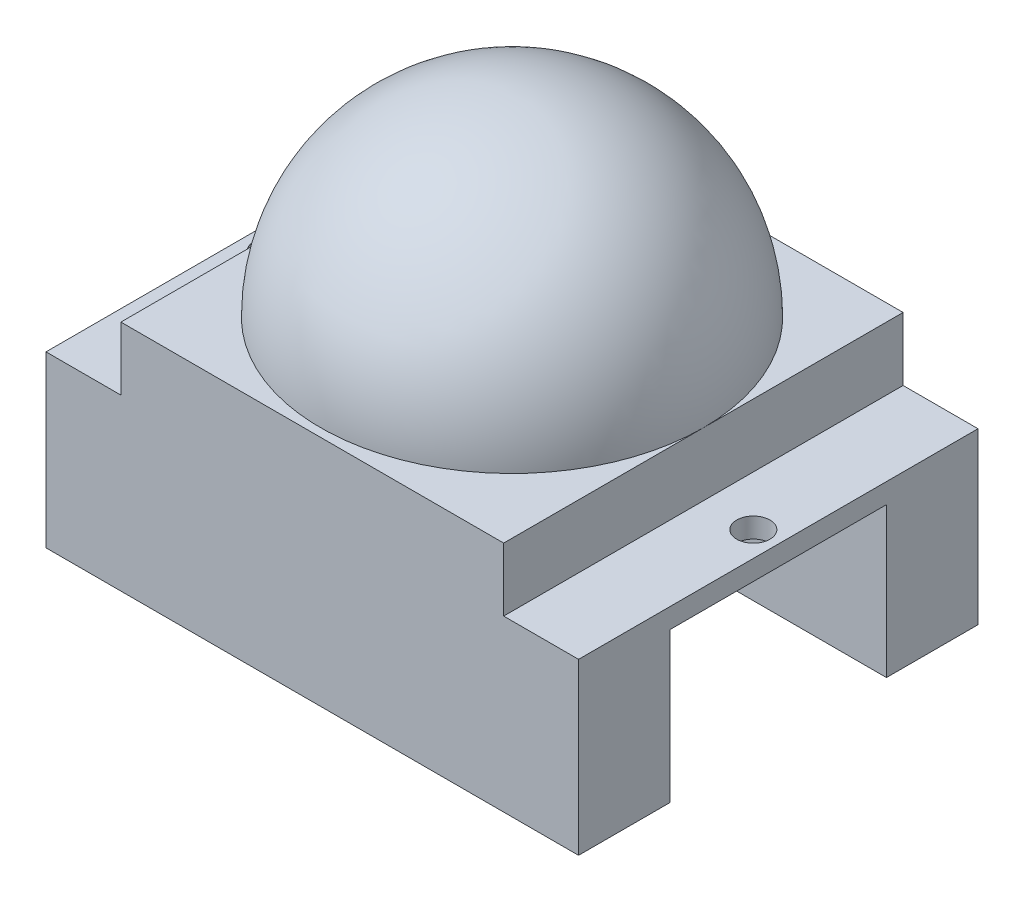
SolidWorks part; units mm, degrees
material "铜"
ref_plane "前视基准面" through (0, 0, 0) normal (0, 0, 1) x (1, 0, 0)
ref_plane "上视基准面" through (0, 0, 0) normal (0, 1, 0) x (1, 0, 0)
ref_plane "右视基准面" through (0, 0, 0) normal (1, 0, 0) x (0, 0, -1)
sketch "草图1" plane through (0, 0, 0) normal (0, 1, 0) x (1, 0, 0)
  line L1 (-16, 12) -> (16, 12)
  line L2 (-16, 12) -> (-16, -12)
  line L3 (-16, -12) -> (16, -12)
  line L4 (16, 12) -> (16, -12)
  line L5 (-16, 12) -> (16, -12) construction
  line L6 (-16, -12) -> (16, 12) construction
  point P0 (0, 0)
  dimension "D1" = 32
  dimension "D2" = 24
extrude "凸台-拉伸1" add sketch "草图1" along normal blind 1.2 contours L2 L1 L4 L3
sketch "草图2" plane through (0, 0, 0) normal (0, 1, 0) x (1, 0, 0)
  line L0 (-11.5, 12) -> (-11.5, -12)
  line L1 (-16, 12) -> (16, 12) construction
  line L2 (-16, -12) -> (16, -12) construction
  line L3 (-11.5, -12) -> (11.5, -12)
  line L4 (11.5, -12) -> (11.5, 12)
  line L5 (11.5, 12) -> (-11.5, 12)
  dimension "D1" = 4.5
  dimension "D2" = 4.5
extrude "凸台-拉伸2" add sketch "草图2" along normal blind 5
sketch3d "3D草图1"
  point P0 (-8.6177, 5, 0.6971)
ref_plane "基准面2" through (0, 5, 0) normal (0, 1, 0) x (1, 0, 0)
sketch "草图5" plane through (0, 0, 0) normal (0, 0, 1) x (1, 0, 0)
  line L0 (0, 5) -> (11.5, 5)
  line L1 (12.65, 5) -> (-12.65, 5) construction
  line L3 (11.5, 5) -> (-11.5, 5) construction
  line L4 (0, 5) -> (0, 21.3297) construction
  line L5 (0, 16.5) -> (0, 5)
  arc A0 (11.5, 5) -> (0, 16.5) centre (0, 5) ccw
  dimension "D1" = 23
sketch3d "3D草图2"
  line L1 (0, -2.1556, 0) -> (0, 17.0185, 0) construction
revolve "旋转5" add sketch "草图5" angle 360 about L4
sketch "草图6" plane through (0, 0, 0) normal (0, 1, 0) x (1, 0, 0)
  line L0 (-16, -12) -> (16, -12)
  line L1 (16, -12) -> (16, -6.5)
  line L2 (16, 12) -> (16, -12) construction
  line L3 (16, -6.5) -> (-16, -6.5)
  line L4 (-16, 12) -> (-16, -12) construction
  line L5 (-16, -6.5) -> (-16, -12)
  line L6 (-16, 6.5) -> (-16, 12)
  line L7 (-16, 12) -> (16, 12)
  line L8 (16, 12) -> (16, 6.5)
  line L9 (16, 6.5) -> (-16, 6.5)
  line L10 (-16, -19.5) -> (-16, 6.5)
  line L11 (-16, 0) -> (16, 0) construction
  point P19 (-16, -6.5)
  dimension "D1" = 5.5
  dimension "D2" = 5.5
extrude "凸台-拉伸5" add sketch "草图6" against normal blind 9 contours L9 L8 L7 L6 | L3 L5 L0 L1
sketch "草图8" plane through (0, 0, 0) normal (0, 1, 0) x (1, 0, 0)
  line L0 (-16, -6.5) -> (-16, 6.5) construction
  line L1 (16, -19.5) -> (16, 6.5)
  line L2 (-16, 0) -> (16, 0) construction
  circle A2 centre (-14.5, 0) radius 1
  circle A3 centre (14.5, 0) radius 1
  point P10 (16, -6.5)
  dimension "D1" = 2
  dimension "D2" = 2
  dimension "D3" = 1.5
  dimension "D4" = 1.5
extrude "切除-拉伸7" cut sketch "草图8" along normal blind 10 contours A3 | A2
